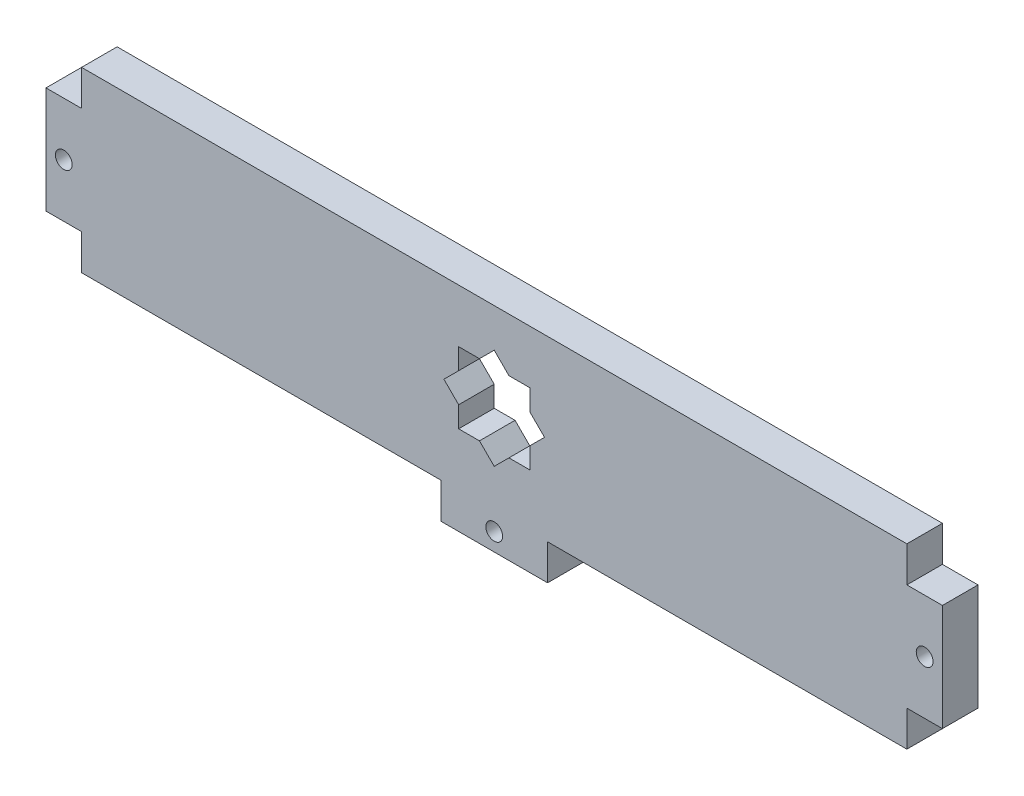
SolidWorks part; units mm, degrees
ref_plane "Front Plane" through (0, 0, 0) normal (0, 0, 1) x (1, 0, 0)
ref_plane "Top Plane" through (0, 0, 0) normal (0, 1, 0) x (1, 0, 0)
ref_plane "Right Plane" through (0, 0, 0) normal (1, 0, 0) x (0, 0, -1)
sketch "Sketch1" plane through (0, 0, 0) normal (0, 0, 1) x (1, 0, 0)
  line L1 (-73.66, -15.875) -> (73.66, -15.875)
  line L2 (-73.66, -15.875) -> (-73.66, 15.875)
  line L3 (-73.66, 15.875) -> (73.66, 15.875)
  line L4 (73.66, -15.875) -> (73.66, 15.875)
  line L5 (-73.66, -15.875) -> (73.66, 15.875) construction
  line L6 (-73.66, 15.875) -> (73.66, -15.875) construction
  point P0 (0, 0)
  dimension "D1" = 31.75
  dimension "D2" = 147.32
extrude "Boss-Extrude1" add sketch "Sketch1" against normal blind 6.35
sketch "Sketch2" plane through (0, 0, 0) normal (0, 0, 1) x (1, 0, 0)
  line L0 (0, -15.875) -> (0, 15.875) construction
  line L1 (-73.66, -15.875) -> (73.66, -15.875) construction
  line L2 (73.66, 15.875) -> (-73.66, 15.875) construction
  line L3 (-73.66, 0) -> (73.66, 0) construction
  line L4 (-73.66, 15.875) -> (-73.66, -15.875) construction
  line L5 (73.66, -15.875) -> (73.66, 15.875) construction
  line L6 (80.01, -9.525) -> (73.66, -9.525)
  line L7 (-80.01, -9.525) -> (-73.66, -9.525)
  line L8 (-80.01, -9.525) -> (-80.01, 9.525)
  line L9 (-80.01, 9.525) -> (-73.66, 9.525)
  line L10 (-73.66, -9.525) -> (-73.66, 9.525)
  line L11 (-80.01, -9.525) -> (-73.66, 9.525) construction
  line L12 (-80.01, 9.525) -> (-73.66, -9.525) construction
  line L13 (80.01, -9.525) -> (80.01, 9.525)
  line L14 (80.01, 9.525) -> (73.66, 9.525)
  line L15 (73.66, -9.525) -> (73.66, 9.525)
  line L17 (-9.525, -22.225) -> (9.525, -22.225)
  line L18 (-9.525, -22.225) -> (-9.525, -15.875)
  line L19 (-9.525, -15.875) -> (9.525, -15.875)
  line L20 (9.525, -22.225) -> (9.525, -15.875)
  line L21 (-9.525, -22.225) -> (9.525, -15.875) construction
  line L22 (-9.525, -15.875) -> (9.525, -22.225) construction
  circle A0 centre (-76.835, 0) radius 1.5
  circle A1 centre (76.835, 0) radius 1.5
  circle A2 centre (0, -19.05) radius 1.5
  point P12 (-76.835, 0)
  point P25 (0, -19.05)
  dimension "D3" = 3
  dimension "D5" = 3
  dimension "D1" = 19.05
  dimension "D2" = 6.35
  dimension "D4" = 0
  dimension "D6" = 19.05
  dimension "D7" = 6.35
extrude "Boss-Extrude2" add sketch "Sketch2" against normal blind 6.35
sketch "Sketch3" plane through (0, 0, 0) normal (0, 0, 1) x (1, 0, 0)
  line L0 (0, -8.9803) -> (2.6303, -6.35)
  line L1 (-6.35, -6.35) -> (-2.6303, -6.35)
  line L2 (-6.35, -6.35) -> (-6.35, -2.6303)
  line L3 (-6.35, 6.35) -> (-2.6303, 6.35)
  line L4 (6.35, -6.35) -> (6.35, -2.6303)
  line L5 (-6.35, -6.35) -> (4.4901, 4.4901) construction
  line L6 (-6.35, 6.35) -> (6.35, -6.35) construction
  line L7 (0, -8.9803) -> (-2.6303, -6.35)
  line L8 (8.9803, 0) -> (6.35, 2.6303)
  line L9 (-8.9803, 0) -> (-6.35, 2.6303)
  line L10 (-6.35, 6.35) -> (-6.35, 2.6303)
  line L11 (6.35, 0) -> (0, 0) construction
  line L12 (2.6303, 6.35) -> (0, 8.9803)
  line L13 (-2.6303, 6.35) -> (0, 8.9803)
  line L14 (-6.35, 0) -> (-8.9803, 0) construction
  line L15 (-6.35, -2.6303) -> (-8.9803, 0)
  line L16 (0, 0) -> (0, 6.35) construction
  line L17 (6.35, -2.6303) -> (8.9803, 0)
  line L18 (6.35, 2.6303) -> (6.35, 6.35)
  line L19 (2.6303, 6.35) -> (6.35, 6.35)
  line L20 (2.6303, -6.35) -> (6.35, -6.35)
  point P0 (0, 0)
  point P7 (0, 0)
  dimension "D1" = 12.7
  dimension "D2" = 12.7
extrude "Cut-Extrude1" cut sketch "Sketch3" against normal up to surface (6.35 mm away) up to face at (-4.0084, -4.7625, -6.35)
